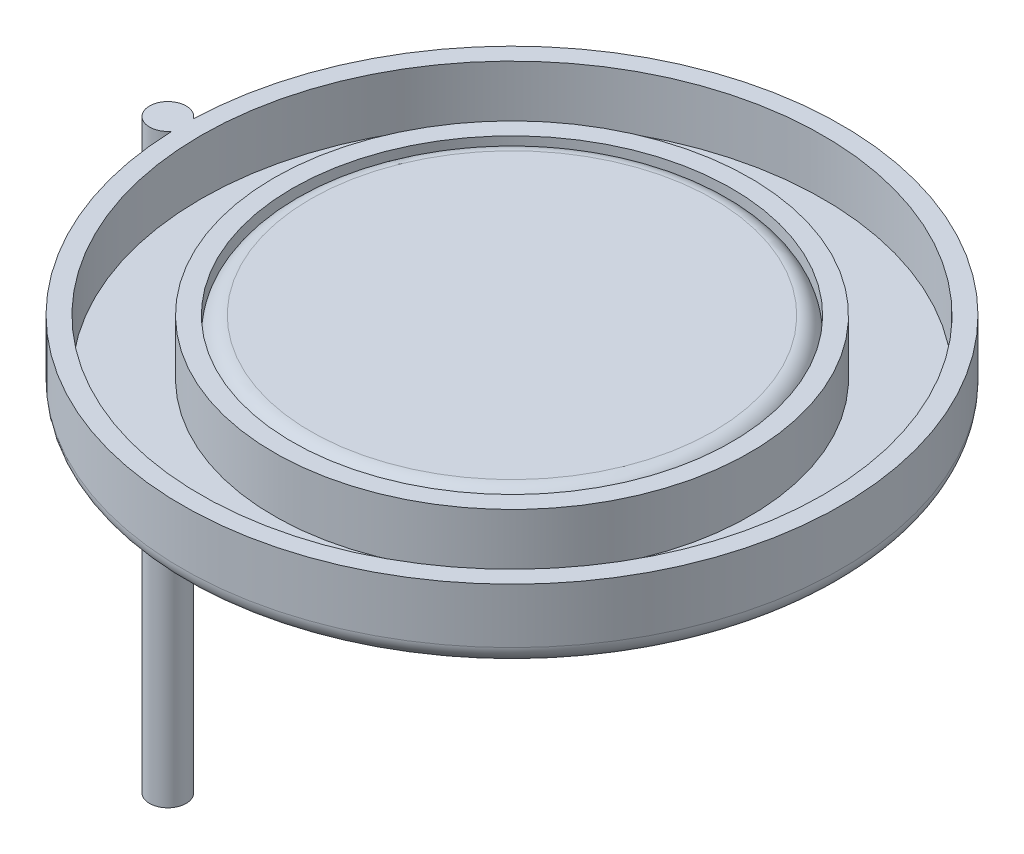
SolidWorks part; units mm, degrees
material "AISI Type 316L stainless steel"
ref_plane "Front Plane" through (0, 0, 0) normal (0, 0, 1) x (1, 0, 0)
ref_plane "Top Plane" through (0, 0, 0) normal (0, 1, 0) x (1, 0, 0)
ref_plane "Right Plane" through (0, 0, 0) normal (1, 0, 0) x (0, 0, -1)
ref_plane "Plane1" through (0, 0, 0) normal (0, 0, 1) x (1, 0, 0)
sketch "Sketch1" plane through (0, 0, 0) normal (0, 0, 1) x (1, 0, 0)
  line L0 (-4.5, 1) -> (-4.5, 0.25)
  line L1 (-4.25, 0) -> (-3.25, 0)
  line L2 (-3, 0.25) -> (-3, 1)
  line L3 (0, 1.05) -> (0, -0.05) construction
  arc A0 (-3.25, 0) -> (-3, 0.25) centre (-3.25, 0.25) ccw
  arc A1 (-4.5, 0.25) -> (-4.25, 0) centre (-4.25, 0.25) ccw
ref_plane "Plane2" through (0, 0, 0) normal (0, 0, 1) x (-1, 0, 0)
sketch "Sketch2" plane through (0, 0, 0) normal (0, 0, 1) x (-1, 0, 0)
  line L0 (-3, 0) -> (-3, -0.75)
  line L1 (-2.75, -1) -> (0, -1)
  line L2 (0, 0.05) -> (0, -1.05) construction
  arc A0 (-3, -0.75) -> (-2.75, -1) centre (-2.75, -0.75) ccw
ref_plane "Plane3" through (0, 1, 0) normal (0, 1, 0) x (1, 0, 0)
sketch "Sketch3" plane through (0, 1, 0) normal (0, 1, 0) x (1, 0, 0)
  circle A0 centre (-4.7, 0) radius 0.25
extrude "Extrude1" add sketch "Sketch3" against normal blind 8
revolve "Revolve-Thin1" add sketch "Sketch2" angle 360 about L2
revolve "Revolve-Thin2" add sketch "Sketch1" angle 360 about L3
